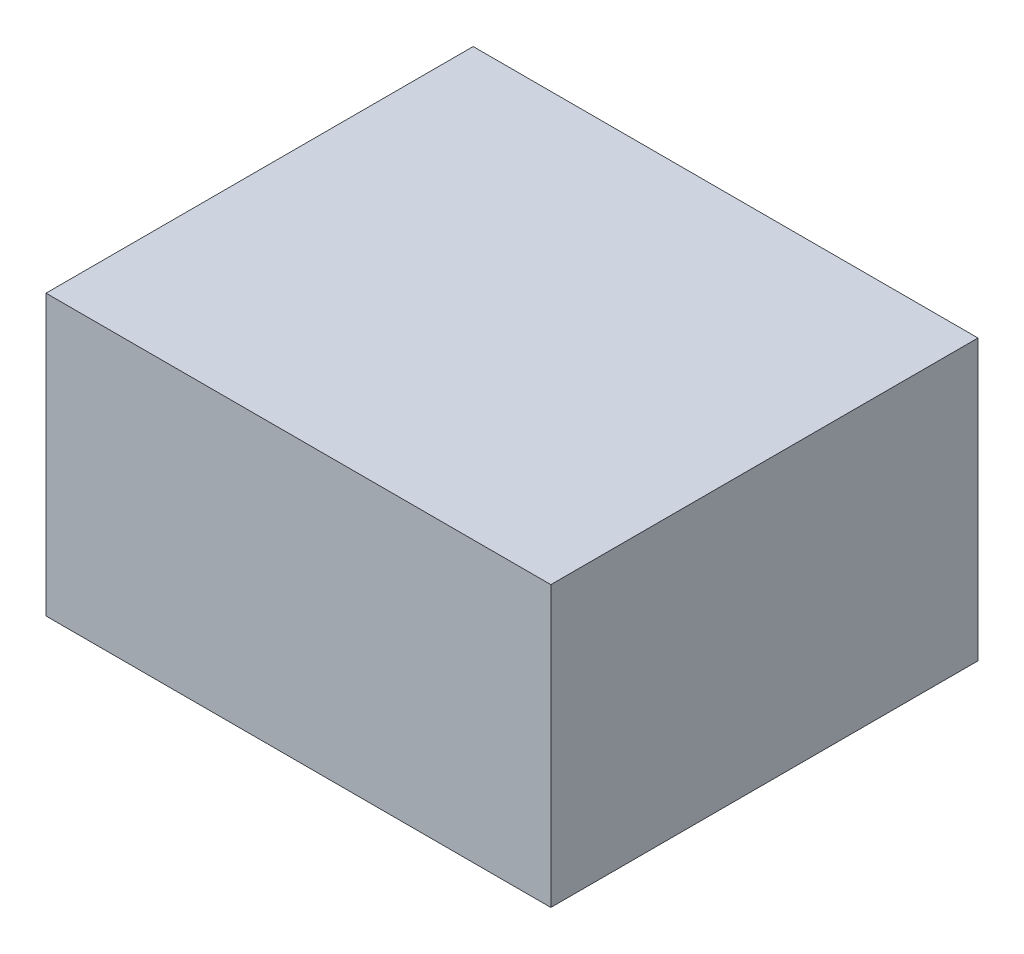
SolidWorks part; units mm, degrees
ref_plane "Спереди" through (0, 0, 0) normal (0, 0, 1) x (1, 0, 0)
ref_plane "Сверху" through (0, 0, 0) normal (0, 1, 0) x (1, 0, 0)
ref_plane "Справа" through (0, 0, 0) normal (1, 0, 0) x (0, 0, -1)
sketch "Эскиз1" plane through (0, 0, 0) normal (0, 1, 0) x (1, 0, 0)
  line L1 (-55.7134, 24.063) -> (9.2866, 24.063)
  line L2 (-55.7134, 24.063) -> (-55.7134, -30.937)
  line L3 (-55.7134, -30.937) -> (9.2866, -30.937)
  line L4 (9.2866, 24.063) -> (9.2866, -30.937)
extrude "Бобышка-Вытянуть1" add sketch "Эскиз1" along normal blind 35
sketch "Эскиз2" plane through (0, 35, 0) normal (0, 1, 0) x (1, 0, 0)
  line L0 (-55.7134, 24.063) -> (-55.2134, 24.063)
  line L1 (9.2866, 24.063) -> (-55.7134, 24.063) construction
  line L2 (-55.2134, 23.563) -> (-55.2134, -29.0633)
  line L3 (-55.7134, -30.937) -> (9.2866, -30.937) construction
  line L4 (-55.7134, -30.937) -> (-55.7134, -30.437)
  line L5 (-55.7134, 24.063) -> (-55.7134, -30.937) construction
  line L6 (-55.2134, -29.0633) -> (-55.2134, -30.437)
  line L7 (-55.2134, -30.437) -> (8.7866, -30.437)
  line L8 (8.7866, -30.437) -> (8.7866, 23.563)
  line L9 (8.7866, 23.563) -> (-55.2134, 23.563)
  point P0 (-23.2134, -3.437)
  point P6 (-55.2134, -30.937)
  point P15 (-55.2134, -30.437)
extrude "Вырез-Вытянуть1" cut sketch "Эскиз2" against normal blind 34 contours L9 L2 L6 L7 L8
sketch "Эскиз3" plane through (0, 35, 0) normal (0, 1, 0) x (1, 0, 0)
  line L1 (-55.7134, 24.063) -> (9.2866, 24.063)
  line L2 (-55.7134, 24.063) -> (-55.7134, -30.937)
  line L3 (-55.7134, -30.937) -> (9.2866, -30.937)
  line L4 (9.2866, 24.063) -> (9.2866, -30.937)
extrude "Бобышка-Вытянуть2" add sketch "Эскиз3" along normal blind 1
